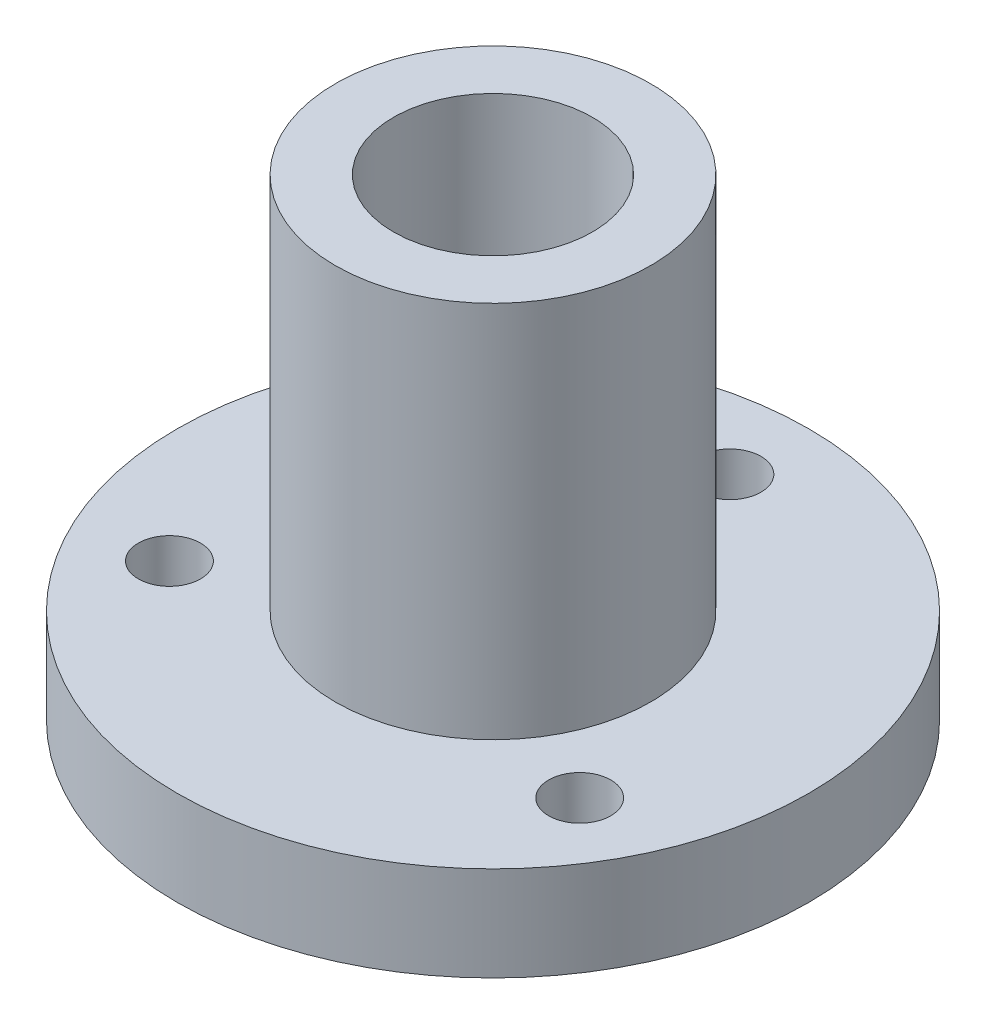
SolidWorks part; units mm, degrees
material "ABS"
ref_plane "Front Plane" through (0, 0, 0) normal (0, 0, 1) x (1, 0, 0)
ref_plane "Top Plane" through (0, 0, 0) normal (0, 1, 0) x (1, 0, 0)
ref_plane "Right Plane" through (0, 0, 0) normal (1, 0, 0) x (0, 0, -1)
sketch "Sketch1" plane through (0, 0, 0) normal (0, 1, 0) x (1, 0, 0)
  circle A0 centre (0, 0) radius 4
  circle A1 centre (0, 0) radius 12.7
  dimension "D1" = 8
  dimension "D2" = 25.4
extrude "Boss-Extrude1" add sketch "Sketch1" along normal blind 3.8
sketch "Sketch2" plane through (0, 3.8, 0) normal (0, 1, 0) x (1, 0, 0)
  circle A0 centre (0, 0) radius 6.34
  circle A1 centre (0, 0) radius 4 construction
  circle A2 centre (0, 0) radius 4
  dimension "D1" = 12.68
extrude "Boss-Extrude2" add sketch "Sketch2" along normal offset from surface (15.2 mm away) 19 up to face at (0, 0, 12.7)
sketch "Sketch3" plane through (0, 0, 0) normal (0, -1, 0) x (1, 0, 0)
  circle A0 centre (0, 0) radius 9.5263 construction
  circle A1 centre (0, -9.5263) radius 1.6
  circle A2 centre (-8.25, 4.7631) radius 1.6
  circle A3 centre (8.25, 4.7631) radius 1.6
  point P11 (0, 0)
  dimension "D1" = 3.2
  dimension "D3" = 16.5
  dimension "D2" = 3
hole_wizard "Tap Drill for M3 Tap1" positions "3DSketch1" profile "Sketch4" hole size "M3" standard "DIN" end condition up to next
sketch3d "3DSketch1"
  point P0 (-8.25, 0, 4.7631)
  point P3 (8.25, 0, 4.7631)
  point P6 (0, 0, -9.5263)
sketch "Sketch4" plane through (-8.25, 0, 4.7631) normal (1, 0, 0) x (0, 0, -1)
  line L0 (0, 0) -> (0, 3.8)
  line L1 (0, 3.8) -> (1.25, 3.8)
  line L2 (1.25, 3.8) -> (1.25, 0)
  line L5 (1.25, 0) -> (0, 0)
  line L11 (0, -6.35) -> (0, 107.95) construction
  dimension "Thru Hole Dia." = 2.5
  dimension "Thru Hole Depth" = 3.8
